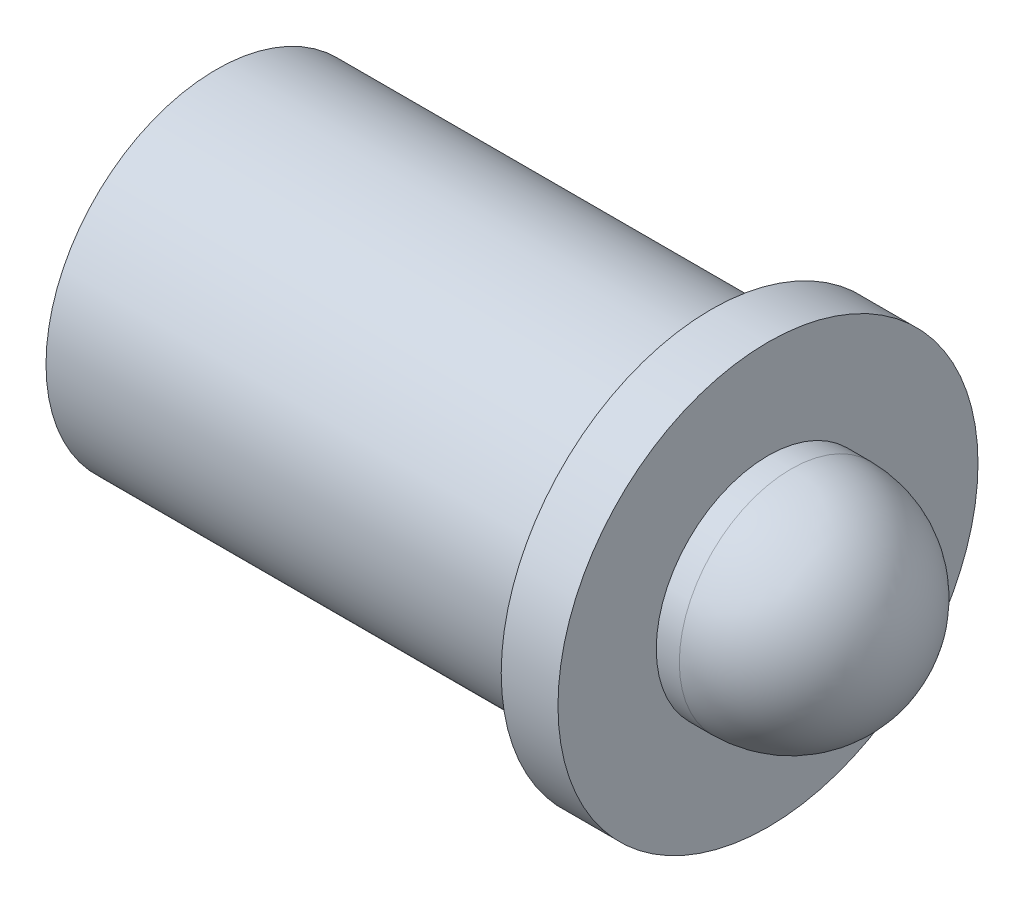
SolidWorks part; units mm, degrees
ref_plane "Front Plane" through (0, 0, 0) normal (0, 0, 1) x (1, 0, 0)
ref_plane "Top Plane" through (0, 0, 0) normal (0, 1, 0) x (1, 0, 0)
ref_plane "Right Plane" through (0, 0, 0) normal (1, 0, 0) x (0, 0, -1)
sketch "Sketch1" plane through (0, 0, 0) normal (0, 0, 1) x (1, 0, 0)
  line L0 (0, 0) -> (12.3444, 0) construction
  line L1 (12.3444, 0) -> (12.3444, 4.699) construction
  line L2 (12.3444, 4.699) -> (11.0744, 4.699)
  line L3 (11.0744, 4.699) -> (11.0744, 3.81)
  line L4 (11.0744, 3.81) -> (0, 3.81)
  line L5 (0, 3.81) -> (0, 0) construction
  line L6 (12.3444, 4.699) -> (12.3444, 2.5)
  line L7 (12.3444, 2.5) -> (10.16, 2.5)
  line L8 (10.16, 2.5) -> (10.16, 3.302)
  line L9 (10.16, 3.302) -> (0, 3.302)
  line L10 (0, 3.302) -> (0, 3.81)
  point P3 (10.16, 2.901)
  dimension "D1" = 12.3444
  dimension "D2" = 3.81
  dimension "D3" = 4.699
  dimension "D4" = 1.27
  dimension "D5" = 3.302
  dimension "D6" = 2.5
  dimension "D7" = 10.16
revolve "Revolve1" add sketch "Sketch1" angle 360 about L0
sketch "Sketch7" plane through (0, 0, 0) normal (0, 0, 1) x (1, 0, 0)
  line L0 (10.16, 3.302) -> (9.2837, 3.302)
  line L1 (10.16, 3.302) -> (0, 3.302) construction
  line L2 (9.2837, 3.302) -> (9.2837, 0)
  line L3 (0, 0) -> (12.3444, 0) construction
  line L4 (9.2837, 0) -> (12.8607, 0)
  line L5 (10.16, 3.302) -> (10.16, 2.5)
  line L6 (10.16, 2.5) -> (12.8607, 2.5)
  line L7 (12.8607, 0) -> (15.3607, 0)
  line L8 (12.8607, 2.5) -> (12.8607, 0) construction
  line L9 (12.8607, 0) -> (12.6975, 0.0005)
  arc A0 (12.8607, 2.5) -> (15.3607, 0) centre (12.8607, 0) cw
  point P9 (13.0348, 2.5)
  point P16 (0, 0)
  point P17 (0, 0)
  dimension "D1" = 3.577
  dimension "D2" = 0.8763
revolve "Revolve4" add sketch "Sketch7" angle 360 about L7
